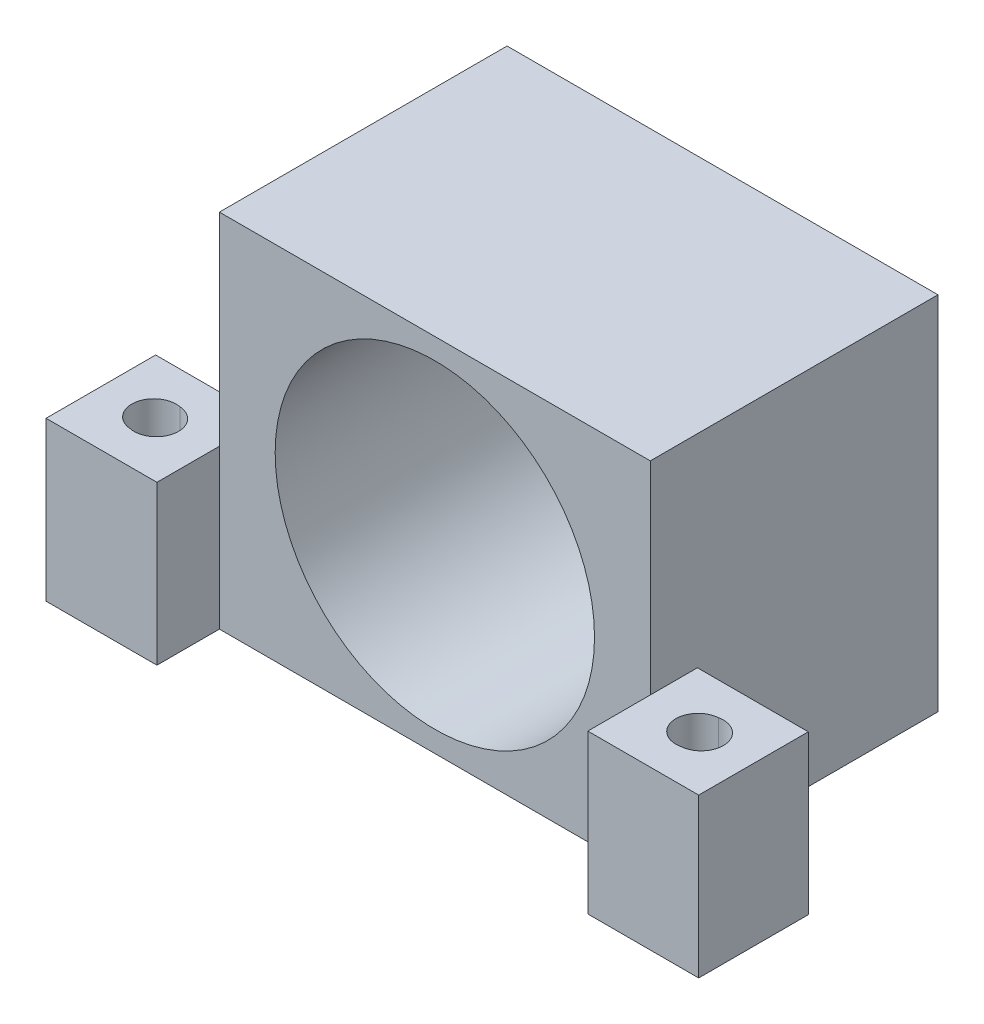
SolidWorks part; units mm, degrees
ref_plane "Front Plane" through (0, 0, 0) normal (0, 0, 1) x (1, 0, 0)
ref_plane "Top Plane" through (0, 0, 0) normal (0, 1, 0) x (1, 0, 0)
ref_plane "Right Plane" through (0, 0, 0) normal (1, 0, 0) x (0, 0, -1)
sketch "Sketch1" plane through (0, 0, 0) normal (0, 0, 1) x (1, 0, 0)
  line L0 (17, -14.25) -> (-17, -14.25)
  line L1 (-17, 14.25) -> (17, 14.25)
  line L2 (-17, 14.25) -> (-17, -14.25)
  line L3 (-17, 0) -> (17, 0) construction
  line L4 (17, 14.25) -> (17, -14.25)
  line L5 (0, 14.25) -> (0, -14.25) construction
  dimension "D2" = 34
  dimension "D3" = 28.5
extrude "Boss-Extrude1" add sketch "Sketch1" along normal blind 22.7
sketch "Sketch3" plane through (0, 0, 22.7) normal (0, 0, 1) x (1, 0, 0)
  circle A0 centre (0, 0) radius 12.6
  dimension "D1" = 25.2
extrude "Cut-Extrude1" cut sketch "Sketch3" against normal blind 19
sketch "Sketch5" plane through (0, 0, 3.7) normal (0, 0, 1) x (1, 0, 0)
  line L0 (13.102, 0) -> (-13.563, 0) construction
  line L1 (0, 12.3911) -> (0, -11.6995) construction
  line L2 (-11.4215, -11.4215) -> (11.4215, 11.4215) construction
  line L3 (10.5106, -10.5106) -> (-10.5106, 10.5106) construction
  circle A0 centre (6.0104, 6.0104) radius 1.625
  circle A1 centre (-6.0104, 6.0104) radius 1.625
  circle A2 centre (6.0104, -6.0104) radius 1.625
  circle A3 centre (-6.0104, -6.0104) radius 1.625
  circle A4 centre (0, 0) radius 8.5 construction
  circle A5 centre (0, 0) radius 3.75
  point P20 (0, 0)
  point P21 (0, 0)
  dimension "D1" = 3.25
  dimension "D2" = 17
  dimension "D3" = 7.5
  dimension "D4" = 45
  dimension "D5" = 45
extrude "Cut-Extrude2" cut sketch "Sketch5" against normal through all
sketch "Sketch7" plane through (0, 0, 22.7) normal (0, 0, 1) x (1, 0, 0)
  line L0 (0, 15.1888) -> (0, -15.3037) construction
  line L1 (-17, -1.75) -> (-25.75, -1.75)
  line L2 (-17, -1.75) -> (-17, -14.25)
  line L3 (-17, -14.25) -> (-25.75, -14.25)
  line L4 (-25.75, -1.75) -> (-25.75, -14.25)
  line L5 (17, -1.75) -> (25.75, -1.75)
  line L6 (17, -1.75) -> (17, -14.25)
  line L7 (17, -14.25) -> (25.75, -14.25)
  line L8 (25.75, -1.75) -> (25.75, -14.25)
  line L9 (17, -14.25) -> (17, 14.25) construction
  line L13 (-17, 14.25) -> (-17, -14.25) construction
  line L14 (-17, -14.25) -> (17, -14.25) construction
  dimension "D1" = 12.5
  dimension "D2" = 8.75
extrude "Boss-Extrude2" add sketch "Sketch7" along normal blind 4.93 and the other way blind 3.72
sketch "Sketch8" plane through (0, -1.75, 0) normal (0, 1, 0) x (1, 0, 0)
  line L0 (21.375, -27.63) -> (21.375, -18.98) construction
  line L1 (25.75, -27.63) -> (17, -27.63) construction
  line L2 (25.75, -18.98) -> (17, -18.98) construction
  line L3 (25.75, -23.305) -> (-25.75, -23.305) construction
  line L4 (25.75, -18.98) -> (25.75, -27.63) construction
  line L5 (-25.75, -18.98) -> (-25.75, -27.63) construction
  line L6 (0, 0) -> (0, -23.3809) construction
  circle A0 centre (21.375, -23.305) radius 1.75
  circle A1 centre (-21.375, -23.305) radius 1.75
  point P17 (21.375, -23.305)
  dimension "D1" = 3.5
extrude "Cut-Extrude3" cut sketch "Sketch8" against normal through all
sketch "Sketch9" plane through (0, -14.25, 0) normal (0, -1, 0) x (1, 0, 0)
  circle A0 centre (-21.375, 23.305) radius 3.25
  circle A1 centre (21.375, 23.305) radius 3.25
  dimension "D1" = 6.5
extrude "Cut-Extrude4" cut sketch "Sketch9" against normal blind 3.175
sketch "Sketch11" plane through (0, 0, 0) normal (0, 0, -1) x (-1, 0, 0)
  line L0 (-11.0405, 11.0405) -> (11.0405, -11.0405) construction
  line L1 (12.8573, 12.8573) -> (-12.8573, -12.8573) construction
  line L2 (-15.1803, 0) -> (19.6713, 0) construction
  line L3 (0, 16.5749) -> (0, -19.4111) construction
  circle A0 centre (-6.0104, 6.0104) radius 1.625 construction
  circle A1 centre (-6.0104, -6.0104) radius 1.625 construction
  circle A2 centre (6.0104, 6.0104) radius 1.625 construction
  circle A3 centre (6.0104, -6.0104) radius 1.625 construction
  circle A4 centre (0, 0) radius 8.5 construction
  circle A5 centre (0, 0) radius 3.75 construction
  circle A6 centre (6.0104, 6.0104) radius 2.8
  circle A7 centre (6.0104, -6.0104) radius 2.8
  circle A8 centre (-6.0104, -6.0104) radius 2.8
  circle A9 centre (-6.0104, 6.0104) radius 2.8
  point P24 (0, 0)
  point P25 (0, 0)
  dimension "D1" = 3.25
  dimension "D2" = 17
  dimension "D3" = 7.5
  dimension "D4" = 5.6
  dimension "D5" = 45
  dimension "D6" = 45
extrude "Cut-Extrude5" cut sketch "Sketch11" against normal blind 10 draft 45
extrude "Cut-Extrude6" cut sketch "Sketch12" against normal blind 50
sketch "Sketch12" plane through (132.274, 1.25, 24.7763) normal (0, 1, 0) x (1, 0, 0)
  line L1 (-149.324, -31.2437) -> (-115.324, -31.2437) construction
  line L4 (-132.559, -64.5637) -> (-132.559, 1.6963) construction
  circle A0 centre (-111.629, 2.4013) radius 1.651
  circle A1 centre (-111.629, -64.8887) radius 1.651
  circle A2 centre (-153.489, -64.8887) radius 1.651
  circle A3 centre (-153.489, 2.4013) radius 1.651
extrude "Cut-Extrude7" cut sketch "Sketch13" against normal blind 50
sketch "Sketch13" plane through (-132.274, 1.25, 87.2637) normal (0, 1, 0) x (-1, 0, 0)
  line L1 (-149.324, -31.3337) -> (-115.324, -31.3337) construction
  line L4 (-132.324, -65.6137) -> (-132.324, 1.6863) construction
  circle A0 centre (-110.734, 2.3213) radius 1.651
  circle A1 centre (-110.734, -64.9887) radius 1.651
  circle A2 centre (-153.914, -64.9887) radius 1.651
  circle A3 centre (-153.914, 2.3213) radius 1.651
extrude "Cut-Extrude8" cut sketch "Sketch14" against normal blind 50
sketch "Sketch14" plane through (132.324, 1.25, 25.7563) normal (0, 1, 0) x (1, 0, 0)
  line L1 (-149.324, -31.1737) -> (-115.324, -31.1737) construction
  line L4 (-132.324, -65.4037) -> (-132.324, 1.8463) construction
  circle A0 centre (-110.734, 2.4813) radius 1.75
  circle A1 centre (-110.734, -64.8287) radius 1.75
  circle A2 centre (-153.914, -64.8287) radius 1.75
  circle A3 centre (-153.914, 2.4813) radius 1.75
extrude "Cut-Extrude12" cut sketch "Sketch18" against normal blind 50
sketch "Sketch18" plane through (-132.324, 1.25, 88.1037) normal (0, 1, 0) x (-1, 0, 0)
  line L1 (-149.324, -31.1737) -> (-115.324, -31.1737) construction
  line L4 (-132.324, -65.4037) -> (-132.324, 1.8463) construction
  circle A0 centre (-110.734, 2.4813) radius 1.651
  circle A1 centre (-110.734, -64.8287) radius 1.651
  circle A2 centre (-153.914, -64.8287) radius 1.651
  circle A3 centre (-153.914, 2.4813) radius 1.651
